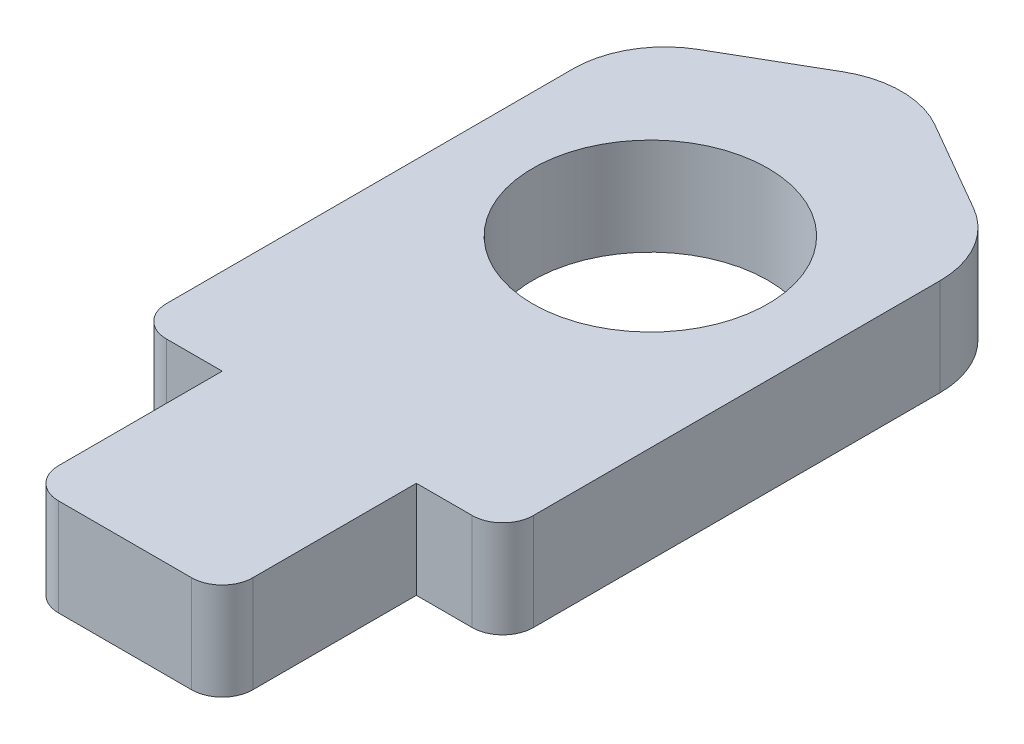
SolidWorks part; units mm, degrees
material "Beech"
ref_plane "Front Plane" through (0, 0, 0) normal (0, 0, 1) x (1, 0, 0)
ref_plane "Top Plane" through (0, 0, 0) normal (0, 1, 0) x (1, 0, 0)
ref_plane "Right Plane" through (0, 0, 0) normal (1, 0, 0) x (0, 0, -1)
sketch "Sketch2" plane through (0, 0, 0) normal (0, 1, 0) x (1, 0, 0)
  line L0 (-6, 5.205) -> (-5.4495, 5.205)
  line L1 (-6, 3.4729) -> (-6, -10.8257)
  line L2 (6, 3.4729) -> (6, -10.8257)
  line L3 (-6, -10.8257) -> (-3.175, -10.8257)
  line L4 (-4.5, 6.071) -> (-1.5, 7.8031)
  line L5 (-3.175, -10.8257) -> (-3.175, -17.1757)
  line L6 (-3.175, -17.1757) -> (3.175, -17.1757)
  line L7 (3.175, -17.1757) -> (3.175, -10.8257)
  line L8 (1.5, 7.8031) -> (4.5, 6.071)
  line L9 (3.175, -10.8257) -> (6, -10.8257)
  line L12 (5.4495, 5.205) -> (6, 5.205)
  circle A0 centre (0, 0) radius 3.845
  arc A1 (-4.5, 6.071) -> (-6, 3.4729) centre (-3, 3.4729) ccw
  arc A2 (4.5, 6.071) -> (6, 3.4729) centre (3, 3.4729) cw
  arc A3 (1.5, 7.8031) -> (-1.5, 7.8031) centre (0, 5.205) ccw
  point P3 (0, 5.205)
  point P14 (0, -17.1757)
  dimension "D1" = 7.69
  dimension "D9" = 3
  dimension "D10" = 3
  dimension "D11" = 3
  dimension "D2" = 5.205
  dimension "D3" = 16.0307
  dimension "D4" = 12
  dimension "D5" = 6.35
  dimension "D6" = 6.35
  dimension "D8" = 30
extrude "MotorMount_Extrude" add sketch "Sketch2" along normal blind 3.175
fillet "MotorMount_CornerFillet" radius 1 4 edges at (6, 1.5875, 10.8257) (-6, 1.5875, 10.8257) (-3.175, 1.5875, 17.1757) (3.175, 1.5875, 17.1757)
equation "\"CageLeftBottomEdge\"=22.11mm"
equation "\"CageLeftTopEdge\"=22.11mm"
equation "\"CageRightBottomEdge\"=21.63mm"
equation "\"CageRightTopEdge\"=21.63mm"
equation "\"CageHeight\"=86.04mm"
equation "\"CageLength\"=73.76mm"
equation "\"CageTopScrewClearance\"=10mm"
equation "\"CageBottomScrewClearance\"=25mm"
equation "\"CageLeftTopDepth\"= 11.65mm"
equation "\"CageLeftBottomDepth\"=11.11mm"
equation "\"CageLeftTopHeight\"=8.56175mm"
equation "\"CageLeftBottomHeight\"=16mm"
equation "\"CageRightTopDepth\"= 11.05mm"
equation "\"CageRightBottomDepth\"=10.58mm"
equation "\"CageRightTopHeight\"=9.6mm"
equation "\"CageRightBottomHeight\"=15.49mm"
equation "\"CageLeftTopChannelDepth\"=2.41908mm"
equation "\"CageLeftBottomChannelDepth\"=2.588mm"
equation "\"CageLeftChannelHeight\"=11.7mm"
equation "\"CageRightTopChannelDepth\"=2.32mm"
equation "\"CageRightBottomChannelDepth\"=2.318mm"
equation "\"CageRightChannelHeight\"=10mm"
equation "\"CageChanRelHeight\"=23.99mm"
equation "\"CageChanRelDepth\"=5.492mm"
equation "\"CageChamberRadius\"=16.261mm"
equation "\"CageScrewDiameter\"=4.8mm"
equation "\"CageSetScrewDiameter\"=3.5mm"
equation "\"CageAxleRadius\"=6.639mm"
equation "\"CageAxleKeyHeight\"=1.619mm"
equation "\"CageAxleKeyWidth\"=2.662mm"
equation "\"CageHoseWindowWidth\"=16.29mm"
equation "\"CageHoseWindowHeight\"=26.5mm"
equation "\"CageHoseWindow-Edge\"=8.89mm"
equation "\"CageScrew-VerticalEdge\"=5.0mm"
equation "\"CageScrew-HorizontalEdge\"=7.5mm"
equation "\"CageScrew-HoseCornerScrewEdge\"=4.45mm"
equation "\"CageAxle-BottomEdge\"=56.05mm"
equation "\"CageAxle-FrontEdge\"=46.03mm"
equation "\"CageBackSetScrew-Axle\"=40mm"
equation "\"CageFrontSetScrew-Axle\"=22mm"
equation "\"CageVelocityWindow-BackEdge\"=34.8mm"
equation "\"CageVelocityWindow-BottomEdge\"=27.55mm"
equation "\"CageVelocityWindowHeight\"=22.29mm"
equation "\"CageVelocityWindowWidth\"=12.61mm"
equation "\"TriggerSlot-BottomEdge\"=6.35mm"
equation "\"TriggerSlot-FrontEdge\"=15mm"
equation "\"TriggerSlotSize\"=6.7mm"
equation "\"TriggerRackOffset\"=.236224in"
equation "\"TriggerSlotSizeInt\"=.25in"
equation "\"MotorMountLegLength\"=.25in"
equation "\"GearOffset\"=.264907in"
equation "\"TriggerSlotSpacing\"=.25in"
equation "\"whitemotordepth\"=11.27mm"
equation "\"whitemotorbackdepth\"=3.845mm"
equation "\"whitemotoraxledepth\" = 3.5mm"
equation "\"whitemotoraxleoffset\"=11.4mm"
equation "\"whitemotorwidth\"=12.07mm"
equation "\"whitemotorheight\"=16.68mm"
equation "\"whitemotorcylinderlength\" =13.04mm"
equation "\"whitemotorcylinderradius\"=3.845mm"
equation "\"whitemotorcylinderoffset\"=2.35mm"
equation "\"whitemotorcutoutlength\"=1.88mm"
equation "\"whitemotorouterrad\"=5mm"
equation "\"whitemotorinnerrad\"=2.95mm"
equation "\"D1@Sketch2\"=\"whitemotorcylinderradius\"*2"
equation "\"D2@Sketch2\"=\"whitemotoraxleoffset\"-\"whitemotorcylinderradius\"-\"whitemotorcylinderoffset\""
equation "\"D3@Sketch2\"=\"elasticdepth\"+.005in+\"TriggerRackOffset\"+\"GearOffset\""
equation "\"D5@Sketch2\"=\"TriggerSlotSizeInt\""
equation "\"D6@Sketch2\"=\"MotorMountLegLength\""
equation "\"motormountwidth\"=12mm"
equation "\"D4@Sketch2\"=\"motormountwidth\""
equation "\"TriggerMiniSlotWidth\"=3.5mm"
equation "\"TriggerRackWidth\"=6.5mm"
equation "\"elasticracklength\"=2in"
equation "\"elasticrackpegsize\"=.25in"
equation "\"elasticrackpegbuffer\"=.125in"
equation "\"elasticrackpegspacing\"=1.76476378in"
equation "\"elasticbaybuffer\"=.25in"
equation "\"elasticdepth\"=.125in"
equation "\"motormountcornerfillet\"=3mm"
equation "\"D10@Sketch2\"=\"motormountcornerfillet\""
equation "\"elasticbaydepth\"=.75in"
equation "\"pandiscradius\"=14in"
equation "\"towermaterialwidth\"=.25in"
equation "\"towerslotlength\"=.5in"
equation "\"towermarkerspace\"=5in"
equation "\"towerslothorizoffset\"=1in"
equation "\"towerslothorizspacing\"=2in"
equation "\"towerslotvertoffset\"=3in"
equation "\"towerslotvertspacing\"=1in"
equation "\"towerheight\"=12in"
equation "\"towerupslot\"=1in"
equation "\"toweraxle\"=.5in"
equation "\"stepperouterrad\"=10mm"
equation "\"stepperscrewsize\"=3.45mm"
equation "\"stepperscrewc2c\"=49.5mm"
equation "\"stepperdepthoffset\"=24mm"
equation "\"stepperhorizoffset\"=22.91mm"
equation "\"shaftslotOD\"=18.8mm"
equation "\"shaftslotID\"=13.28mm"
equation "\"shaftkeywidth\"=2.67mm"
equation "\"shaftkeydepth\"=1.8mm"
equation "\"shaftcollartotaldepth\"=12.5mm"
equation "\"shaftsquaredepth\"=6mm"
equation "\"shaftsetscrewsize\"=3.5mm"
equation "\"shaftkeytightdepth\"=1.85mm"
equation "\"shaftslottightID\"=12.78mm"
equation "\"shaftsetscrewoffset\"=9mm"
equation "\"cagecollartotaldepth\"=10mm"
equation "\"cagecollartotalwidth\"=35mm"
equation "\"cagecollarbasedepth\"=4mm"
equation "\"gearhubintdiam\"=30mm"
equation "\"gearhubintwid\"=15mm"
equation "\"towerspeedwidth\"=2in"
equation "\"towerspeedheight\"=8in"
equation "\"towerspeedgap\"=2in"
equation "\"stepperaxleflat\"=.037in"
equation "\"stepperaxlerad\"=0.11811024in"
equation "\"ajaxaxlesize\"=3.87mm"
equation "\"ajaxinnercut\"=2.3mm"
equation "\"ajaxwidth\"=6.1mm"
equation "\"ajaxdiametral\"=25.8854"
equation "\"ajaxcutoutdepth\"=2.3mm"
equation "\"ajax4020gap\"=29.5mm"
equation "\"ajax4010gap\"=24.5mm"
equation "\"ajax20hubbuffer\"=0.240157in"
equation "\"ajax20hubholeoffset\"=.19685in"
equation "\"ajax20hubholesize\"=.059055in"
equation "\"ajax20cutoutint\"=13.4mm"
equation "\"ajax40hubholesize\"=7.21mm"
equation "\"ajax40hubholeoffset\"=10mm"
equation "\"ajax40hubbuffer\"=.350394in"
equation "\"ajax40cutoutint\"=32.6mm"
equation "\"bearingpandiscrad\"=6.8in"
equation "\"bearingpandiscang\"=48.75deg"
equation "\"bearingclearholedist\"=4.7345in"
equation "\"bearingclearholesize\"=.5in"
equation "\"bearingclearholeang\"=22.5deg"
equation "\"bearingmountholedist\"=4.25in"
equation "\"bearingwirehole\"=1.5in"
equation "\"no6diam\"=.146in"
equation "\"shortconangle\"=20deg"
equation "\"shortconlen\"=.875in"
equation "\"longconlen\"=1.25in"
equation "\"TGMGearFaceDiameter\"=24.40mm"
equation "\"TGMCylinderLength\"=15.00mm"
equation "\"TGMScrewHole-Center\"=8.70mm"
equation "\"TGMScrewHoleDiameter\"=5.04mm"
equation "\"TGMCenterHoleDiameter\"=9.50mm"
equation "\"TGMShaftCollarSideLength\"=19.00mm"
equation "\"TGMShaftCollarDockingDepth\"=7.00mm"
equation "\"towerplatslotoffset\"=1.5in"
equation "\"towermotorpanelheight\"=10in"
equation "\"towerplatdepth\"=2in"
equation "\"ajaxhubdepth\"=.25in"
equation "\"shconangle\"=20deg"
equation "\"shconlen\"=1in"
equation "\"lnconlen\"=1.5in"
equation "\"lnconangle\"=15deg"
